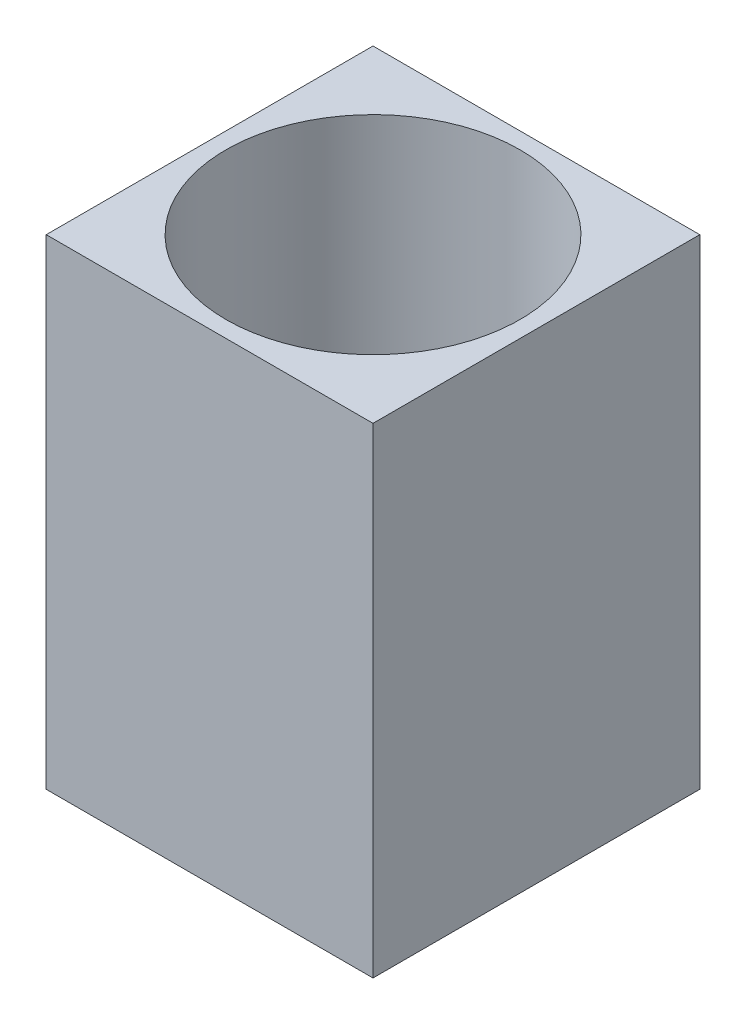
SolidWorks part; units mm, degrees
ref_plane "Front Plane" through (0, 0, 0) normal (0, 0, 1) x (1, 0, 0)
ref_plane "Top Plane" through (0, 0, 0) normal (0, 1, 0) x (1, 0, 0)
ref_plane "Right Plane" through (0, 0, 0) normal (1, 0, 0) x (0, 0, -1)
sketch "Sketch1" plane through (0, 0, 0) normal (0, 1, 0) x (1, 0, 0)
  line L1 (0, 0) -> (10, 0)
  line L2 (0, 0) -> (0, -10)
  line L3 (0, -10) -> (10, -10)
  line L4 (10, 0) -> (10, -10)
  circle A0 centre (5, -5) radius 4.5
  point P8 (5, 0)
  point P10 (0, -5)
  dimension "D3" = 9
  dimension "D1" = 10
  dimension "D2" = 10
extrude "Boss-Extrude1" add sketch "Sketch1" along normal blind 14.7
sketch "Sketch2" plane through (0, 0, 0) normal (0, -1, 0) x (-1, 0, 0)
  line L1 (-10, -10) -> (0, -10)
  line L2 (-10, -10) -> (-10, 0)
  line L3 (-10, 0) -> (0, 0)
  line L4 (0, -10) -> (0, 0)
  circle A0 centre (-5, -5) radius 3.5
  circle A1 centre (-5, -5) radius 4.5 construction
  dimension "D1" = 7
extrude "Boss-Extrude2" add sketch "Sketch2" against normal blind 3
sketch "Sketch3" plane through (0, 0, 0) normal (0, -1, 0) x (-1, 0, 0)
  circle A0 centre (-5, -5) radius 4.5
  circle A1 centre (-5, -5) radius 3.5 construction
  dimension "D1" = 9
extrude "Cut-Extrude1" cut sketch "Sketch3" against normal blind 2
